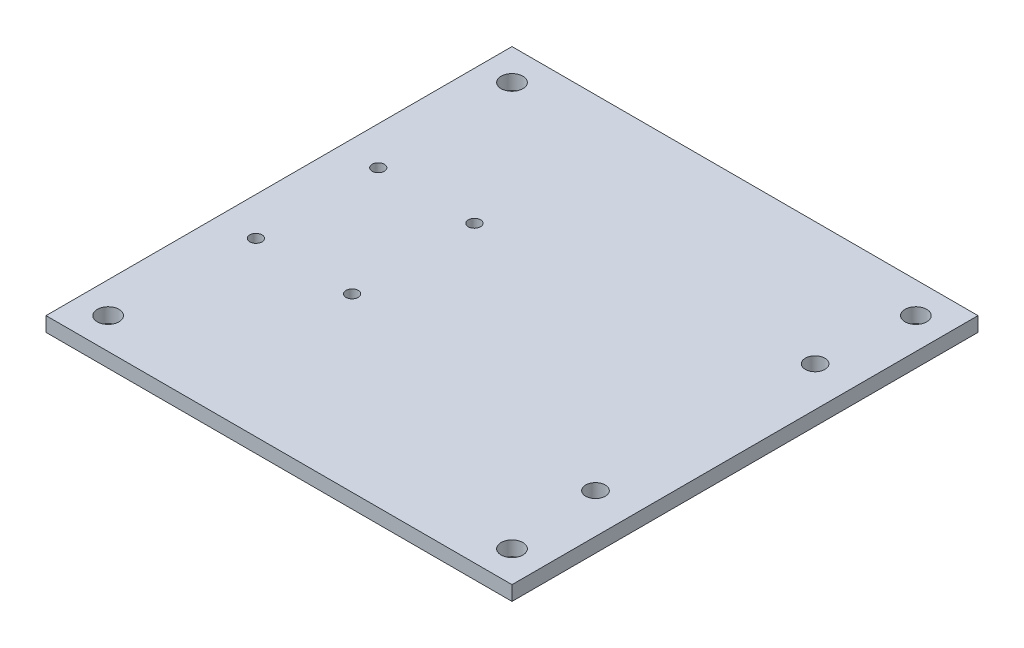
SolidWorks part; units mm, degrees
material "6061 Alloy"
ref_plane "Front Plane" through (0, 0, 0) normal (0, 0, 1) x (1, 0, 0)
ref_plane "Top Plane" through (0, 0, 0) normal (0, 1, 0) x (1, 0, 0)
ref_plane "Right Plane" through (0, 0, 0) normal (1, 0, 0) x (0, 0, -1)
sketch "Sketch2" plane through (0, 0, 0) normal (0, 1, 0) x (1, 0, 0)
  line L0 (0, -25.4) -> (0, 127)
  line L1 (0, 127) -> (152.4, 127)
  line L3 (152.4, -25.4) -> (0, -25.4)
  line L4 (152.4, 127) -> (152.4, -25.4)
  line L5 (0, 50.8) -> (152.4, 50.8) construction
  line L6 (10.16, 116.84) -> (142.24, 116.84) construction
  line L7 (142.24, 116.84) -> (142.24, -15.24) construction
  line L8 (135.0537, 14.8828) -> (139.4194, 14.8828) construction
  line L9 (139.4194, 14.8828) -> (139.4194, 86.7172) construction
  line L10 (142.24, -15.24) -> (10.16, -15.24) construction
  line L11 (10.16, -15.24) -> (10.16, 116.84) construction
  line L12 (12.4515, 70.8) -> (12.4515, 30.8) construction
  line L13 (43.9043, 70.8) -> (43.9043, 30.8) construction
  circle A4 centre (139.4194, 14.8828) radius 3.2004
  circle A5 centre (139.4194, 86.7172) radius 3.2004
  circle A6 centre (142.24, 116.84) radius 3.556
  circle A7 centre (10.16, 116.84) radius 3.556
  circle A8 centre (10.16, -15.24) radius 3.556
  circle A9 centre (142.24, -15.24) radius 3.556
  circle A10 centre (12.4515, 30.8) radius 2
  circle A11 centre (43.9043, 30.8) radius 2
  circle A12 centre (43.9043, 70.8) radius 2
  circle A13 centre (12.4515, 70.8) radius 2
  dimension "D1" = 10.16
extrude "Boss-Extrude1" add sketch "Sketch2" along normal blind 4.7625
